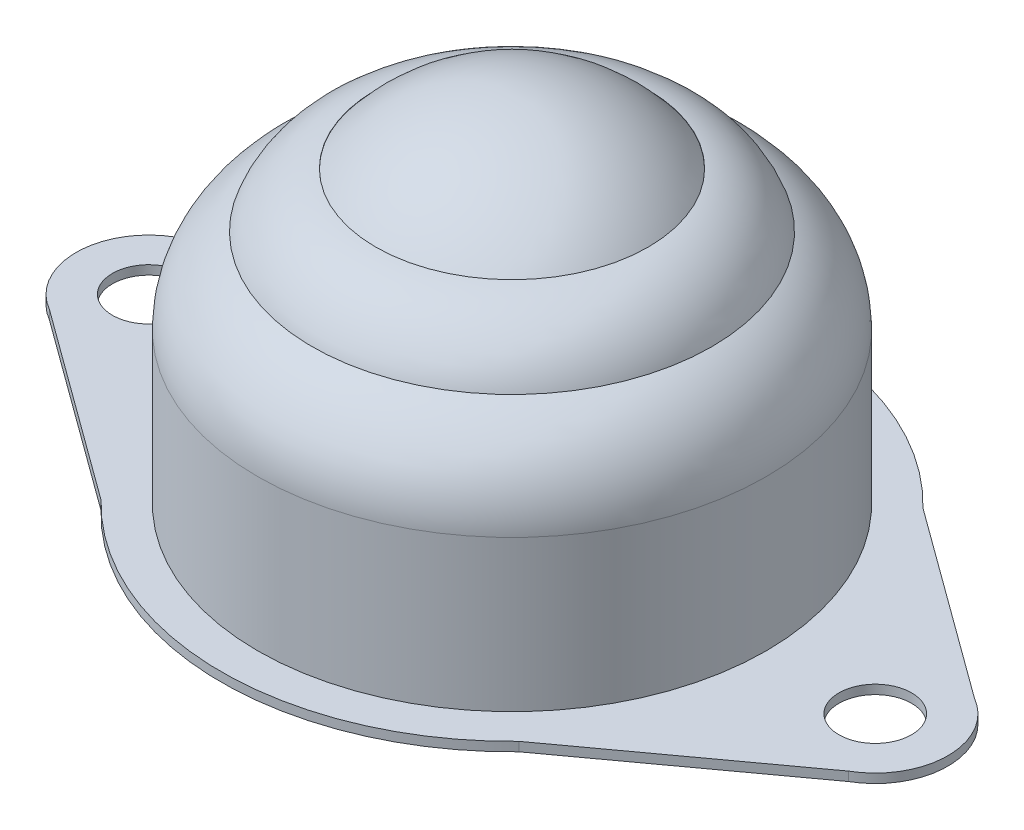
SolidWorks part; units mm, degrees
ref_plane "Alzado" through (0, 0, 0) normal (0, 0, 1) x (1, 0, 0)
ref_plane "Planta" through (0, 0, 0) normal (0, 1, 0) x (1, 0, 0)
ref_plane "Vista lateral" through (0, 0, 0) normal (1, 0, 0) x (0, 0, -1)
sketch "Croquis1" plane through (0, 0, 0) normal (0, 0, 1) x (1, 0, 0)
  line L0 (0, -155.4342) -> (0, 7616.2777) construction
  line L1 (-14, 0) -> (-14, 8.3067)
  line L3 (-14, 0) -> (0, 0)
  line L11 (-13.8, 0.2) -> (0, 0.2)
  line L12 (-13.8, 0.2) -> (-13.8, 8.3067)
  line L13 (-7.5, 16) -> (-7.4642, 15.8032)
  line L14 (0, 0.2) -> (0, 0)
  arc A2 (-14, 8.3067) -> (-11, 13) centre (-8.8288, 8.3067) cw
  arc A3 (-11, 13) -> (-7.5, 16) centre (-6.6818, 11.5038) cw
  arc A6 (-13.8, 8.3067) -> (-10.8381, 12.8537) centre (-8.8288, 8.3067) cw
  arc A7 (-10.8381, 12.8537) -> (-7.4642, 15.8032) centre (-6.6818, 11.5038) cw
  dimension "D7" = 4.57
  dimension "D8" = 5.1712
  dimension "D1" = 14
  dimension "D2" = 11
  dimension "D3" = 7.5
  dimension "D4" = 16
  dimension "D6" = 13
  dimension "D5" = 0.2
revolve "Revolución1" add sketch "Croquis1" angle 360 about L0
sketch "Croquis2" plane through (0, 0, 0) normal (0, -1, 0) x (1, 0, 0)
  line L0 (-11.5, -11.1243) -> (-22, -3.4641)
  line L1 (-22, 3.4641) -> (-11.5, 11.1243)
  line L2 (0, -1000) -> (0, 49000) construction
  line L3 (11.5, -11.1243) -> (22, -3.4641)
  line L4 (22, 3.4641) -> (11.5, 11.1243)
  arc A0 (-11.5, -11.1243) -> (11.5, -11.1243) centre (0, 0) ccw
  circle A1 centre (-20, 0) radius 2
  arc A3 (-22, -3.4641) -> (-22, 3.4641) centre (-20, 0) cw
  circle A4 centre (20, 0) radius 2
  arc A5 (22, -3.4641) -> (22, 3.4641) centre (20, 0) ccw
  arc A6 (11.5, 11.1243) -> (-11.5, 11.1243) centre (0, 0) ccw
  dimension "D1" = 32
  dimension "D3" = 4
  dimension "D4" = 4
  dimension "D2" = 20
  dimension "D5" = 11.5
  dimension "D6" = 22
extrude "Saliente-Extruir1" add sketch "Croquis2" along normal blind 0.5
sketch "Croquis4" plane through (0, 0, 0) normal (0, 0, 1) x (1, 0, 0)
  line L2 (0, 19.5) -> (0, 0)
  arc A1 (0, 19.5) -> (0, 0) centre (0, 9.75) ccw
  dimension "D1" = 19.5
revolve "Revolución2" add sketch "Croquis4" angle 360 about L2
